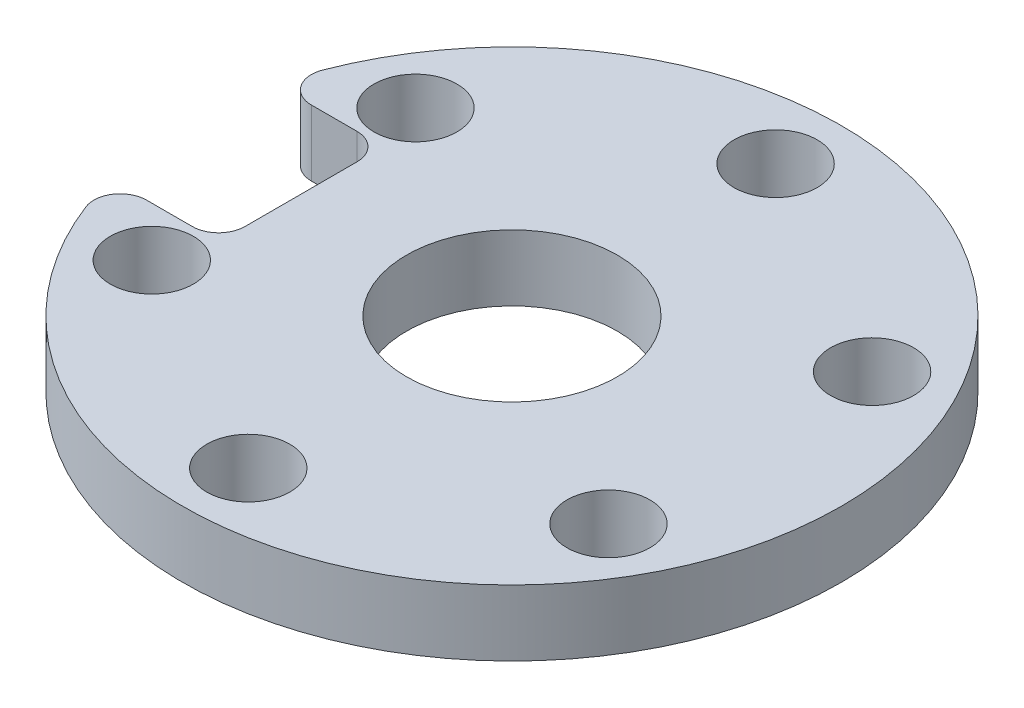
SolidWorks part; units mm, degrees
ref_plane "前视基准面" through (0, 0, 0) normal (0, 0, 1) x (1, 0, 0)
ref_plane "上视基准面" through (0, 0, 0) normal (0, 1, 0) x (1, 0, 0)
ref_plane "右视基准面" through (0, 0, 0) normal (1, 0, 0) x (0, 0, -1)
other "Configuration Table"
sketch "草图1" plane through (0, 0, 0) normal (0, 1, 0) x (1, 0, 0)
  circle A0 centre (0, 0) radius 25
  circle A1 centre (0, 0) radius 20 construction
  circle A2 centre (0, 20) radius 3.15
  circle A3 centre (17.3205, 10) radius 3.15
  circle A4 centre (17.3205, -10) radius 3.15
  circle A5 centre (0, -20) radius 3.15
  circle A6 centre (-17.3205, -10) radius 3.15
  circle A7 centre (-17.3205, 10) radius 3.15
  point P19 (0, 0)
  dimension "D1" = 50
  dimension "D2" = 40
  dimension "D3" = 6.3
  dimension "D4" = 6
extrude "凸台-拉伸1" add sketch "草图1" along normal blind 5
sketch "草图2" plane through (0, 0, 0) normal (0, 1, 0) x (1, 0, 0)
  line L1 (-25, 6.25) -> (-16, 6.25)
  line L2 (-25, 6.25) -> (-25, -6.25)
  line L3 (-25, -6.25) -> (-16, -6.25)
  line L4 (-16, 6.25) -> (-16, -6.25)
  circle A0 centre (0, 0) radius 25 construction
  point P4 (-16, 0)
  dimension "D1" = 12.5
  dimension "D2" = 9
extrude "切除-拉伸3" cut sketch "草图2" along normal through all
fillet "圆角1" radius 2 4 edges at (-16, 2.5, 6.25) (-24.2061, 2.5, 6.25) (-24.2061, 2.5, -6.25) (-16, 2.5, -6.25)
sketch "草图3" plane through (0, 5, 0) normal (0, 1, 0) x (1, 0, 0)
  circle A0 centre (0, 0) radius 8
  dimension "D1" = 16
extrude "切除-拉伸4" cut sketch "草图3" against normal through all
